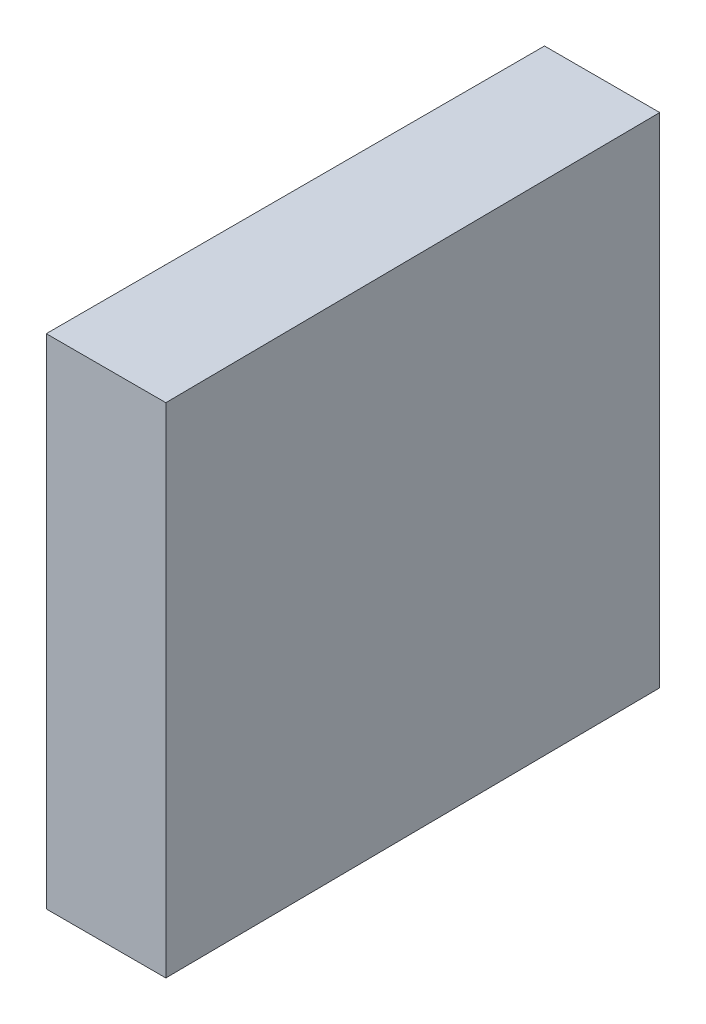
SolidWorks part; units mm, degrees
ref_plane "前视基准面" through (0, 0, 0) normal (0, 0, 1) x (1, 0, 0)
ref_plane "上视基准面" through (0, 0, 0) normal (0, 1, 0) x (1, 0, 0)
ref_plane "右视基准面" through (0, 0, 0) normal (1, 0, 0) x (0, 0, -1)
sketch "草图1" plane through (0, 0, 0) normal (0, 1, 0) x (1, 0, 0)
  line L0 (-12.1202, 0) -> (19.0875, 0) construction
  line L1 (0, 6.25) -> (0, -6.25)
  line L2 (0, -6.25) -> (3, -6.25)
  line L3 (3, -6.25) -> (2.8909, 6.25)
  line L4 (0, 6.25) -> (2.8909, 6.25)
  point P5 (0, 0)
  dimension "D1" = 3
  dimension "D2" = 12.5
  dimension "D3" = 0.5
extrude "凸台-拉伸1" add sketch "草图1" along normal blind 12.5
